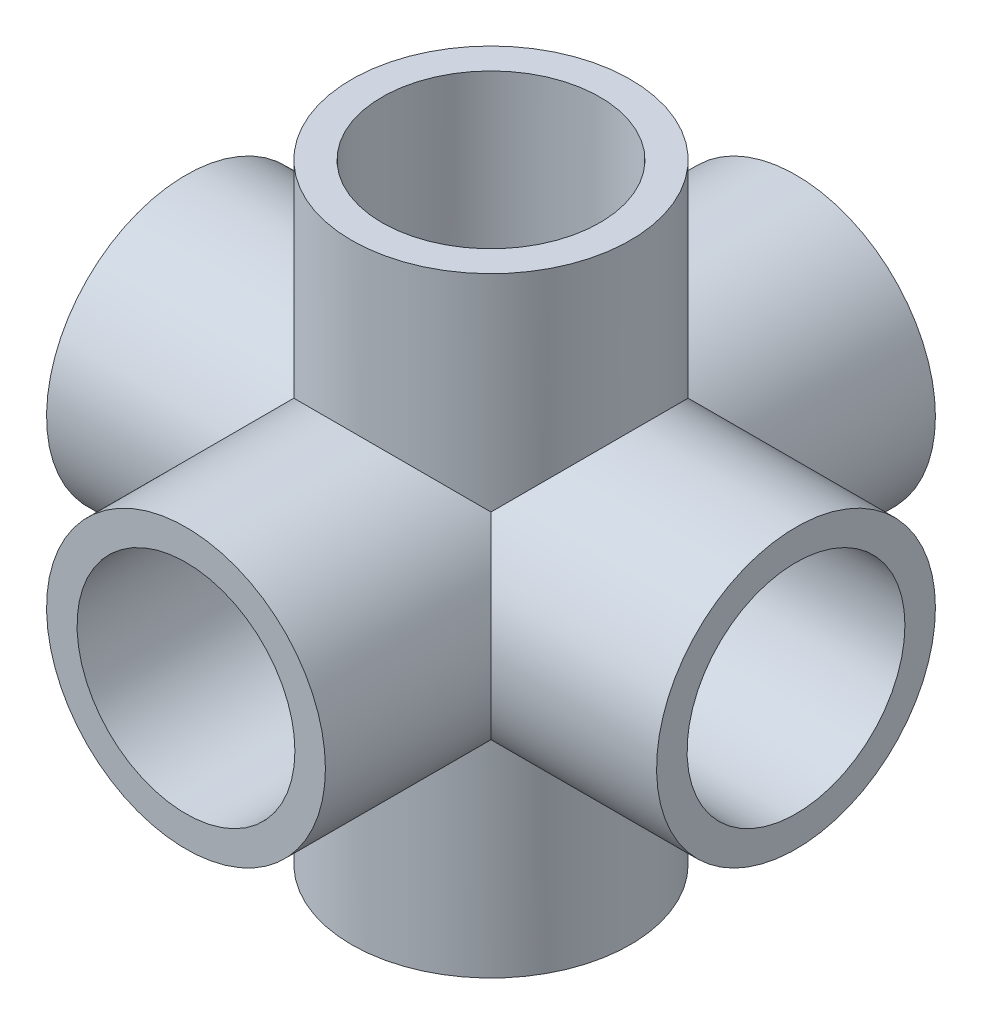
SolidWorks part; units mm, degrees
ref_plane "前视基准面" through (0, 0, 0) normal (0, 0, 1) x (1, 0, 0)
ref_plane "上视基准面" through (0, 0, 0) normal (0, 1, 0) x (1, 0, 0)
ref_plane "右视基准面" through (0, 0, 0) normal (1, 0, 0) x (0, 0, -1)
other "Configuration Table"
sketch "草图1" plane through (0, 0, 0) normal (0, 0, 1) x (1, 0, 0)
  circle A0 centre (0, 0) radius 12.5
  circle A1 centre (0, 0) radius 16
  dimension "D1" = 25
  dimension "D2" = 32
extrude "凸台-拉伸1" add sketch "草图1" along normal mid plane 70
sketch "草图2" plane through (0, 0, 0) normal (1, 0, 0) x (0, 0, -1)
  circle A0 centre (0, 0) radius 16
  circle A1 centre (0, 0) radius 12.5
  dimension "D1" = 32
  dimension "D2" = 25
extrude "凸台-拉伸2" add sketch "草图2" along normal mid plane 70
sketch "草图4" plane through (0, 0, 0) normal (0, 1, 0) x (1, 0, 0)
  circle A2 centre (0, 0) radius 16
  circle A3 centre (0, 0) radius 12.5
  dimension "D1" = 32
  dimension "D2" = 25
extrude "凸台-拉伸3" add sketch "草图4" along normal mid plane 70
